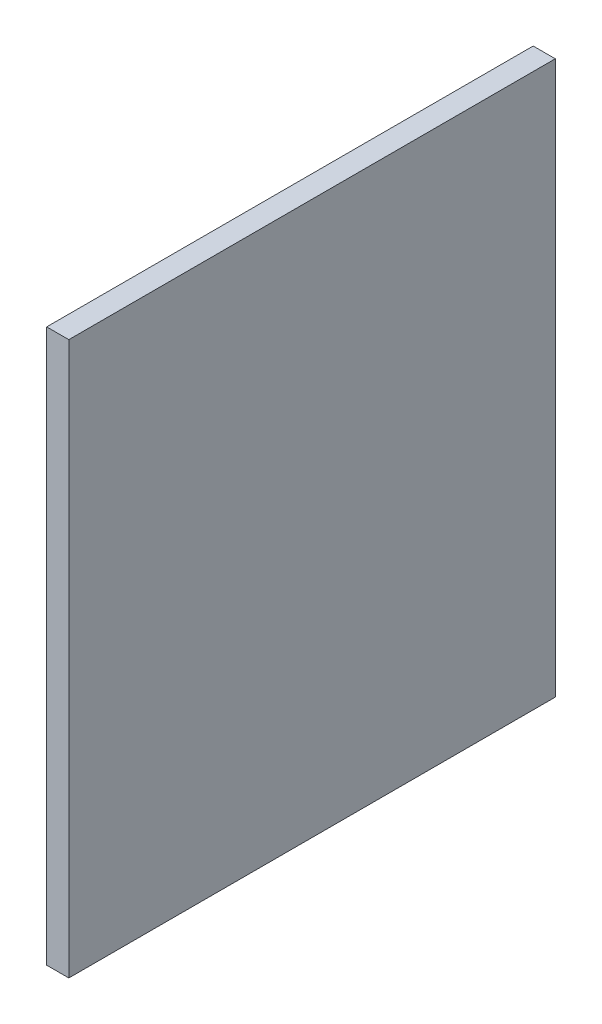
SolidWorks part; units mm, degrees
material "Teck"
ref_plane "Plan de face" through (0, 0, 0) normal (0, 0, 1) x (1, 0, 0)
ref_plane "Plan de dessus" through (0, 0, 0) normal (0, 1, 0) x (1, 0, 0)
ref_plane "Plan de droite" through (0, 0, 0) normal (1, 0, 0) x (0, 0, -1)
sketch "Esquisse1" plane through (0, 0, 0) normal (1, 0, 0) x (0, 0, -1)
  line L1 (-220, -250) -> (220, -250)
  line L2 (-220, -250) -> (-220, 250)
  line L3 (-220, 250) -> (220, 250)
  line L4 (220, -250) -> (220, 250)
  line L5 (-220, -250) -> (220, 250) construction
  line L6 (-220, 250) -> (220, -250) construction
  point P0 (0, 0)
  dimension "D1" = 440
  dimension "D2" = 500
extrude "Boss.-Extru.1" add sketch "Esquisse1" along normal blind 20
